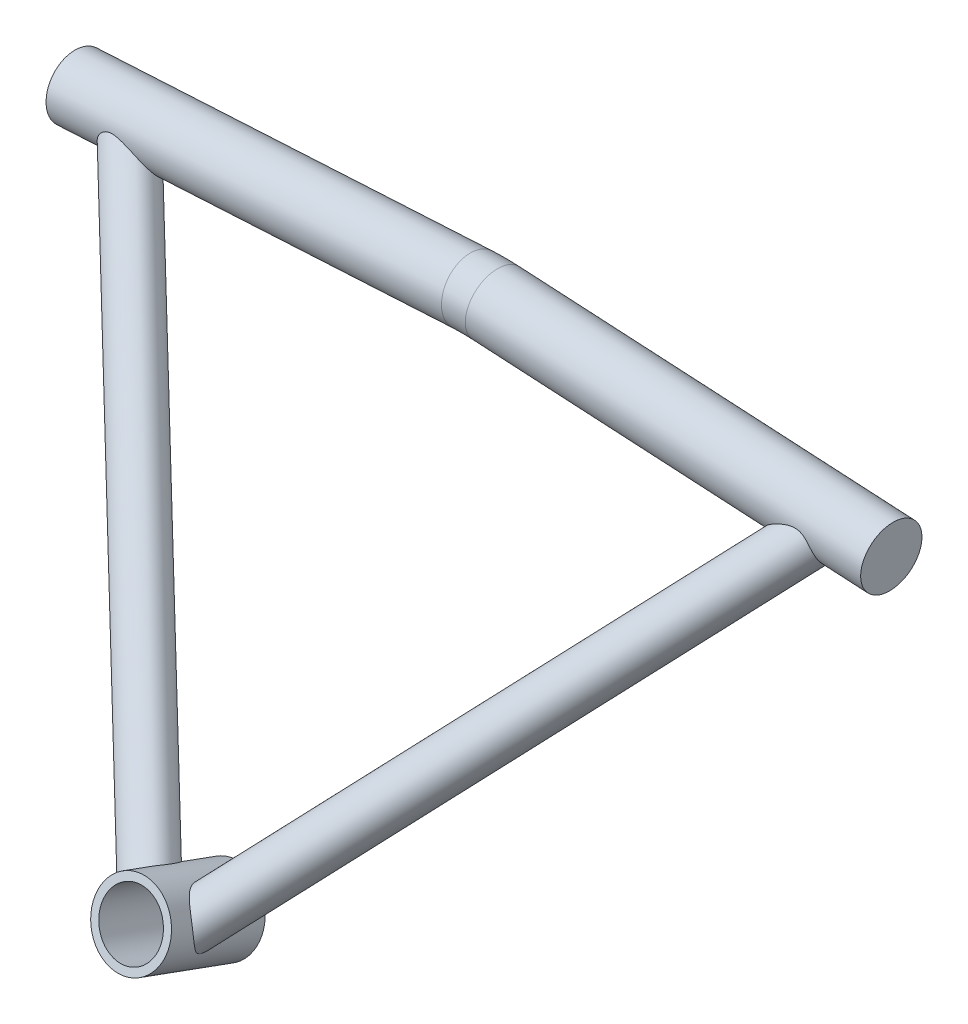
SolidWorks part; units mm, degrees
material "AISI 4130 Steel, normalized at 870C"
ref_plane "Front Plane" through (0, 0, 0) normal (0, 0, 1) x (1, 0, 0)
ref_plane "Top Plane" through (0, 0, 0) normal (0, 1, 0) x (1, 0, 0)
ref_plane "Right Plane" through (0, 0, 0) normal (1, 0, 0) x (0, 0, -1)
sketch "Sketch3" plane through (0, 0, 0) normal (0, 1, 0) x (1, 0, 0)
  line L0 (-5.08, -6.35) -> (5.08, -6.35) construction
  line L2 (0, -88.2205) -> (0, 88.2205) construction
  line L3 (5.08, 0) -> (-5.08, 0) construction
  dimension "D1" = 5.08
  dimension "D2" = 10.16
  dimension "D3" = 6.35
  dimension "D4" = 10.16
  dimension "D5" = 5.08
ref_plane "Plane1" through (0, 3.1441, 3.6169) normal (0, 0.6561, 0.7547) x (1, 0, 0)
ref_plane "Plane3" through (0, 0, 0) normal (0, 0.342, 0.9397) x (-1, 0, 0)
sketch "Sketch1" plane through (0, 0, 0) normal (0, 0.342, 0.9397) x (1, 0, 0)
  circle A0 centre (0, 0) radius 15.875
  dimension "D1" = 31.75
extrude "Boss-Extrude1" add sketch "Sketch1" along normal mid plane 41.402 contours A0
sketch "Sketch4" plane through (0, 3.1441, 3.6169) normal (0, 0.6561, 0.7547) x (1, 0, 0)
  line L0 (-5.08, -4.166) -> (-143.484, 193.4954)
  line L2 (0, -55) -> (0, 55) construction
  dimension "D2" = 35
  dimension "D3" = 241.3
sweep "Sweep1" add path "Sketch4" circular profile diameter 19.05 parameters "D3"=19.05
sketch "Sketch15" plane through (0, 3.1441, 3.6169) normal (0, 0.6561, 0.7547) x (1, 0, 0)
  line L0 (5.08, -4.166) -> (143.484, 193.4954)
  line L1 (0, -55) -> (0, 55) construction
  dimension "D1" = 241.3
  dimension "D2" = 35
sweep "Sweep2" add path "Sketch15" circular profile diameter 19.05 parameters "D3"=19.05
sketch "Sketch36" plane through (-138.1179, 148.8686, -129.4095) normal (-0.5736, 0.6182, -0.5374) x (0.8191, 0.4394, -0.3687)
  circle A0 centre (-6.5024, -4.8578) radius 7.9375
  dimension "D1" = 15.875
extrude "Cut-Extrude2" cut sketch "Sketch36" against normal up to surface (251.5099 mm away)
sketch "Sketch37" plane through (138.1179, 148.8686, -129.4095) normal (0.5736, 0.6182, -0.5374) x (0.8191, -0.4394, 0.3687)
  circle A0 centre (6.5024, -4.8578) radius 7.9375
  dimension "D1" = 15.875
extrude "Cut-Extrude3" cut sketch "Sketch37" against normal up to surface (226.8376 mm away)
sketch "Sketch77" plane through (0, 7.0802, 19.4526) normal (0, 0.342, 0.9397) x (1, 0, 0)
  circle A1 centre (0, 0) radius 15.875
extrude "Boss-Extrude2" add sketch "Sketch77" against normal up to surface (41.402 mm away) up to face at (0, -21.9978, -14.023)
sketch "Sketch2" plane through (0, -7.0802, -19.4526) normal (0, -0.342, -0.9397) x (-1, 0, 0)
  circle A0 centre (0, 0) radius 12.7
  dimension "D1" = 25.4
extrude "Cut-Extrude1" cut sketch "Sketch2" against normal up to next
ref_plane "Plane2" through (0, 0, -127) normal (0, 0, 1) x (1, 0, 0)
sketch "Sketch40" plane through (-106.934, 0, -127) normal (0, 0, 1) x (1, 0, 0)
  line L2 (106.934, -101.5068) -> (106.934, 101.5068) construction
  line L3 (101.9947, 159.6287) -> (-62.0894, 150.498)
  line L4 (111.8733, 159.6287) -> (275.9574, 150.498)
  arc A0 (101.9947, 159.6287) -> (111.8733, 159.6287) centre (106.934, 70.866) cw
  point P0 (106.934, 159.766)
  point P7 (106.934, 159.766)
  dimension "D1" = 164.338
  dimension "D3" = 88.9
  dimension "D2" = 164.338
  dimension "D4" = 9.8786
sweep "Sweep3" add path "Sketch40" circular profile diameter 25.4 parameters "D3"=25.4
